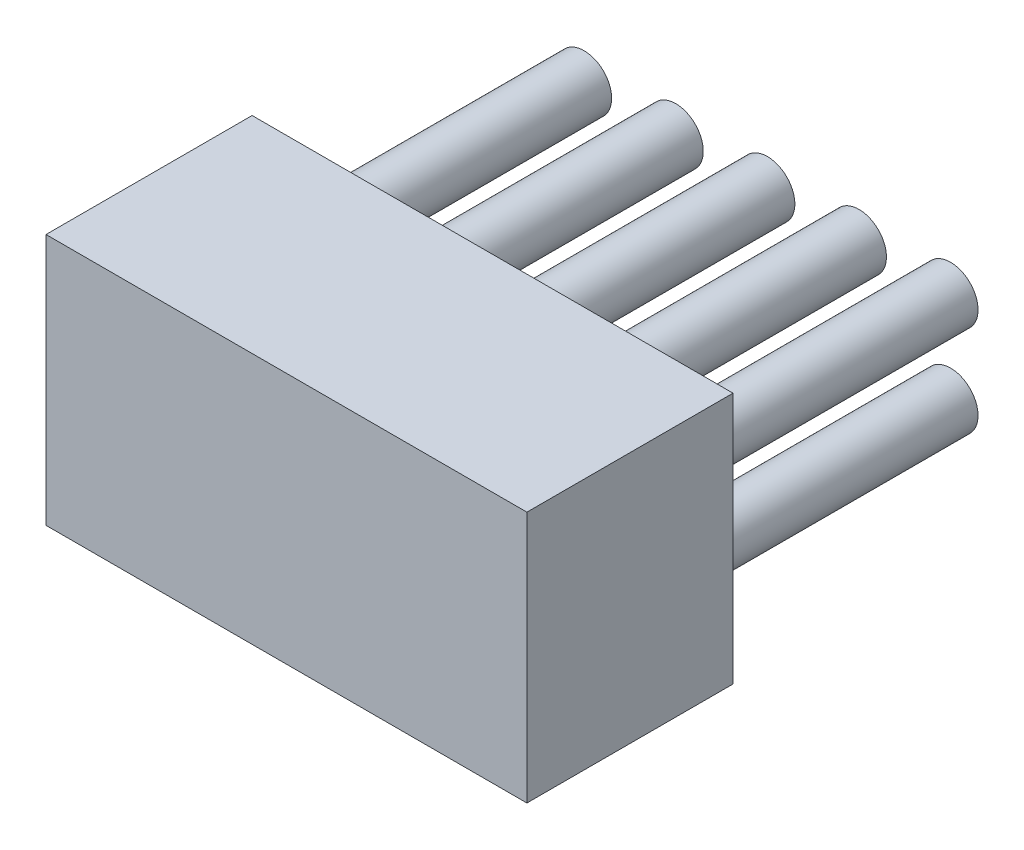
SolidWorks part; units mm, degrees
ref_plane "Front Plane" through (0, 0, 0) normal (0, 0, 1) x (1, 0, 0)
ref_plane "Top Plane" through (0, 0, 0) normal (0, 1, 0) x (1, 0, 0)
ref_plane "Right Plane" through (0, 0, 0) normal (1, 0, 0) x (0, 0, -1)
sketch "Sketch1" plane through (0, 0, 0) normal (0, 0, 1) x (1, 0, 0)
  line L1 (0, 0) -> (10.5, 0)
  line L2 (0, 0) -> (0, 5.5)
  line L3 (0, 5.5) -> (10.5, 5.5)
  line L4 (10.5, 0) -> (10.5, 5.5)
  dimension "D1" = 10.5
  dimension "D2" = 5.5
extrude "Boss-Extrude1" add sketch "Sketch1" along normal blind 4.5
sketch "Sketch2" plane through (0, 0, 0) normal (0, 0, -1) x (-1, 0, 0)
  line L0 (0, 0) -> (-10.5, 5.5) construction
  line L1 (-9.25, 3.75) -> (-1.25, 3.75) construction
  line L2 (-9.25, 1.75) -> (-1.25, 1.75) construction
  line L3 (-5.25, 1.75) -> (-5.25, 3.75) construction
  circle A0 centre (-9.25, 3.75) radius 0.6
  circle A1 centre (-9.25, 1.75) radius 0.6
  circle A2 centre (-5.25, 1.75) radius 0.6
  circle A3 centre (-7.25, 1.75) radius 0.6
  circle A4 centre (-7.25, 3.75) radius 0.6
  circle A5 centre (-5.25, 3.75) radius 0.6
  circle A6 centre (-3.25, 3.75) radius 0.6
  circle A7 centre (-1.25, 3.75) radius 0.6
  circle A8 centre (-1.25, 1.75) radius 0.6
  circle A9 centre (-3.25, 1.75) radius 0.6
  point P10 (-5.25, 2.75)
  dimension "D3" = 1.2
  dimension "D1" = 8
  dimension "D2" = 2
  dimension "D4" = 2
  dimension "D5" = 2
extrude "Boss-Extrude2" add sketch "Sketch2" along normal blind 6
